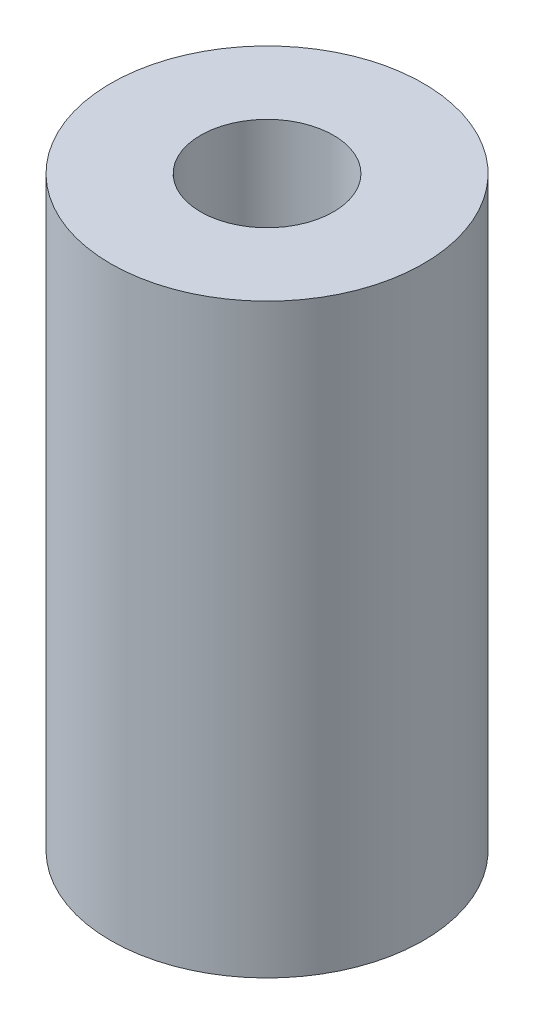
SolidWorks part; units mm, degrees
material "PEI"
ref_plane "Front Plane" through (0, 0, 0) normal (0, 0, 1) x (1, 0, 0)
ref_plane "Top Plane" through (0, 0, 0) normal (0, 1, 0) x (1, 0, 0)
ref_plane "Right Plane" through (0, 0, 0) normal (1, 0, 0) x (0, 0, -1)
sketch "Sketch1" plane through (0, 0, 0) normal (0, 1, 0) x (1, 0, 0)
  circle A0 centre (0, 0) radius 1.7
  circle A1 centre (0, 0) radius 4
  dimension "D1" = 3.4
  dimension "D2" = 8
extrude "Boss-Extrude1" add sketch "Sketch1" along normal blind 15
